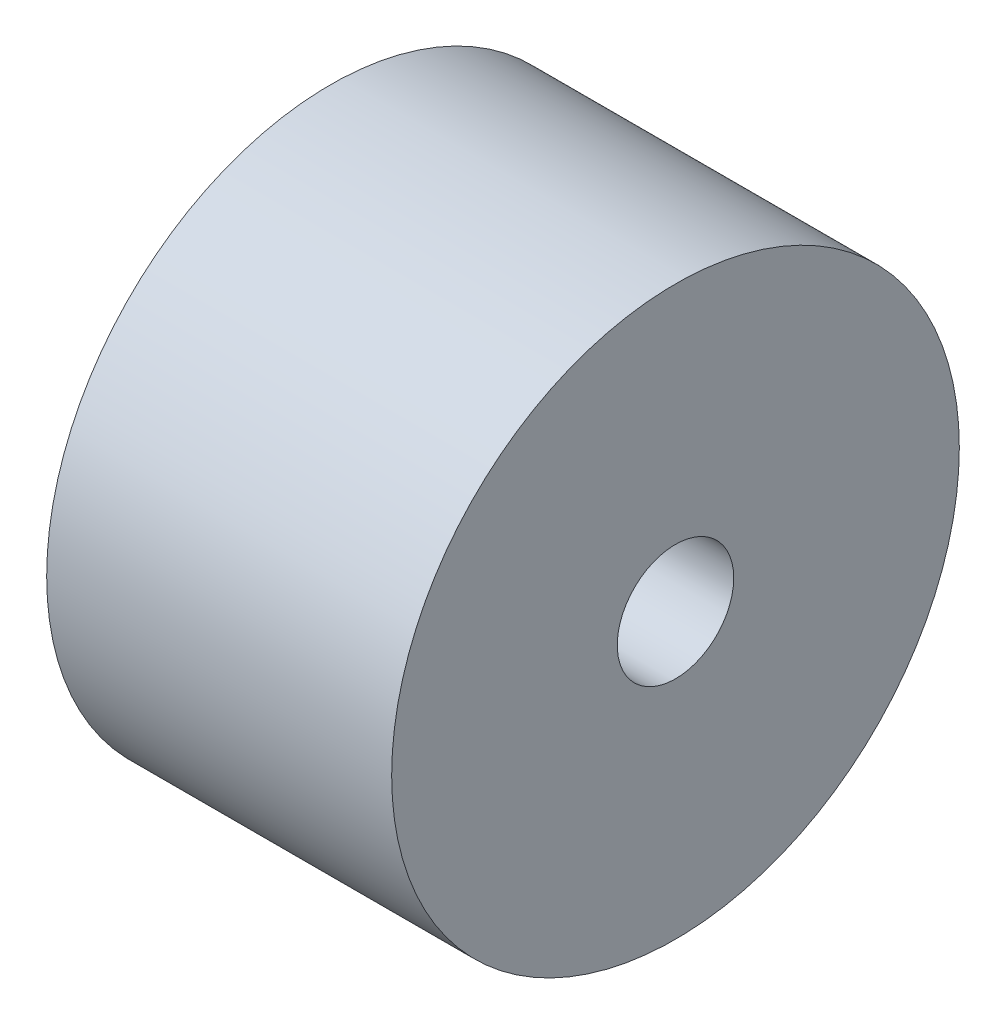
SolidWorks part; units mm, degrees
ref_plane "Front Plane" through (0, 0, 0) normal (0, 0, 1) x (1, 0, 0)
ref_plane "Top Plane" through (0, 0, 0) normal (0, 1, 0) x (1, 0, 0)
ref_plane "Right Plane" through (0, 0, 0) normal (1, 0, 0) x (0, 0, -1)
sketch "Sketch1" plane through (0, 0, 0) normal (0, 0, 1) x (1, 0, 0)
  line L0 (8.255, 0) -> (-8.255, 0) construction
  line L1 (30.255, 0) -> (-30.255, 0) construction
  line L2 (8.255, 0) -> (8.255, 18.1)
  line L3 (8.255, 18.1) -> (30.255, 18.1)
  line L4 (30.255, 18.1) -> (30.255, 0)
  line L5 (8.255, 0) -> (30.255, 0)
  point P4 (0, 0)
  point P8 (0, 0)
  dimension "D1" = 22
  dimension "D2" = 16.51
  dimension "D3" = 18.1
revolve "Revolve1" add sketch "Sketch1" angle 360 about L5
sketch "Sketch2" plane through (8.255, 0, 0) normal (-1, 0, 0) x (0, 0, 1)
  circle A0 centre (0, 0) radius 3.7138
  dimension "D1" = 7.4275
extrude "Cut-Extrude1" cut sketch "Sketch2" against normal blind 8.5725
sketch "Sketch3" plane through (30.255, 0, 0) normal (1, 0, 0) x (0, 0, -1)
  line L0 (-20.8953, -55) -> (-20.8953, -46.1532)
  line L1 (13.175, -55) -> (-13.175, -55) construction
  line L2 (13.175, -55) -> (13.175, 55) construction
  line L3 (13.175, 55) -> (-13.175, 55) construction
  line L4 (-13.175, -55) -> (-13.175, 55) construction
  line L5 (13.175, -55) -> (-13.175, 55) construction
  line L6 (13.175, 55) -> (-13.175, -55) construction
  line L7 (-24.3823, -32.1152) -> (-32.3245, -17.1152)
  line L9 (-5.4548, -55) -> (-5.4548, -44)
  line L11 (5.4547, -44) -> (5.4547, -55)
  line L12 (20.8953, -55) -> (20.8953, -46.1532)
  line L13 (24.3823, -32.1152) -> (32.3245, -17.1152)
  line L14 (55, 0) -> (-55, 0) construction
  line L15 (13.175, -55) -> (-13.175, 55) construction
  line L16 (13.175, 55) -> (-13.175, -55) construction
  line L17 (13.175, 55) -> (-13.175, 55) construction
  line L18 (24.3823, 32.1152) -> (32.3245, 17.1152)
  line L19 (20.8953, 55) -> (20.8953, 46.1532)
  line L20 (5.4547, 44) -> (5.4547, 55)
  line L21 (-5.4548, 55) -> (-5.4548, 44)
  line L22 (-24.3823, 32.1152) -> (-32.3245, 17.1152)
  line L23 (-20.8953, 55) -> (-20.8953, 46.1532)
  arc A15 (32.3245, -17.1152) -> (32.3245, 17.1152) centre (0, 0) ccw
  arc A16 (-5.4548, 55) -> (-20.8953, 55) centre (-13.175, 55) ccw
  arc A17 (-20.8953, -55) -> (-5.4548, -55) centre (-13.175, -55) ccw
  arc A18 (5.4547, -55) -> (20.8953, -55) centre (13.175, -55) ccw
  arc A19 (20.8953, 55) -> (5.4547, 55) centre (13.175, 55) ccw
  arc A20 (-5.4548, -44) -> (5.4547, -44) centre (0, -44) cw
  arc A21 (20.8953, -46.1532) -> (24.3823, -32.1152) centre (50.8953, -46.1532) cw
  arc A22 (-20.8953, -46.1532) -> (-24.3823, -32.1152) centre (-50.8953, -46.1532) ccw
  arc A23 (-20.8953, 46.1532) -> (-24.3823, 32.1152) centre (-50.8953, 46.1532) cw
  arc A24 (20.8953, 46.1532) -> (24.3823, 32.1152) centre (50.8953, 46.1532) ccw
  arc A25 (-5.4548, 44) -> (5.4547, 44) centre (0, 44) ccw
  arc A26 (5.4547, 55) -> (20.8953, 55) centre (13.175, 55) cw
  arc A27 (-20.8953, 55) -> (-5.4548, 55) centre (-13.175, 55) cw
  arc A29 (-32.3245, 17.1152) -> (-32.3245, -17.1152) centre (0, 0) ccw
  dimension "D3" = 15.4405
  dimension "D5" = 7.7203
  dimension "D4" = 30
  dimension "D7" = 15
  dimension "D9" = 110
  dimension "D1" = 73.152
  dimension "D6" = 15
  dimension "D2" = 26.35
  dimension "D8" = 11
sketch "Sketch4" plane through (30.255, 0, 0) normal (1, 0, 0) x (0, 0, -1)
  circle A0 centre (0, 0) radius 3.7138
  dimension "D1" = 7.4275
extrude "Cut-Extrude2" cut sketch "Sketch4" against normal blind 8.5725
